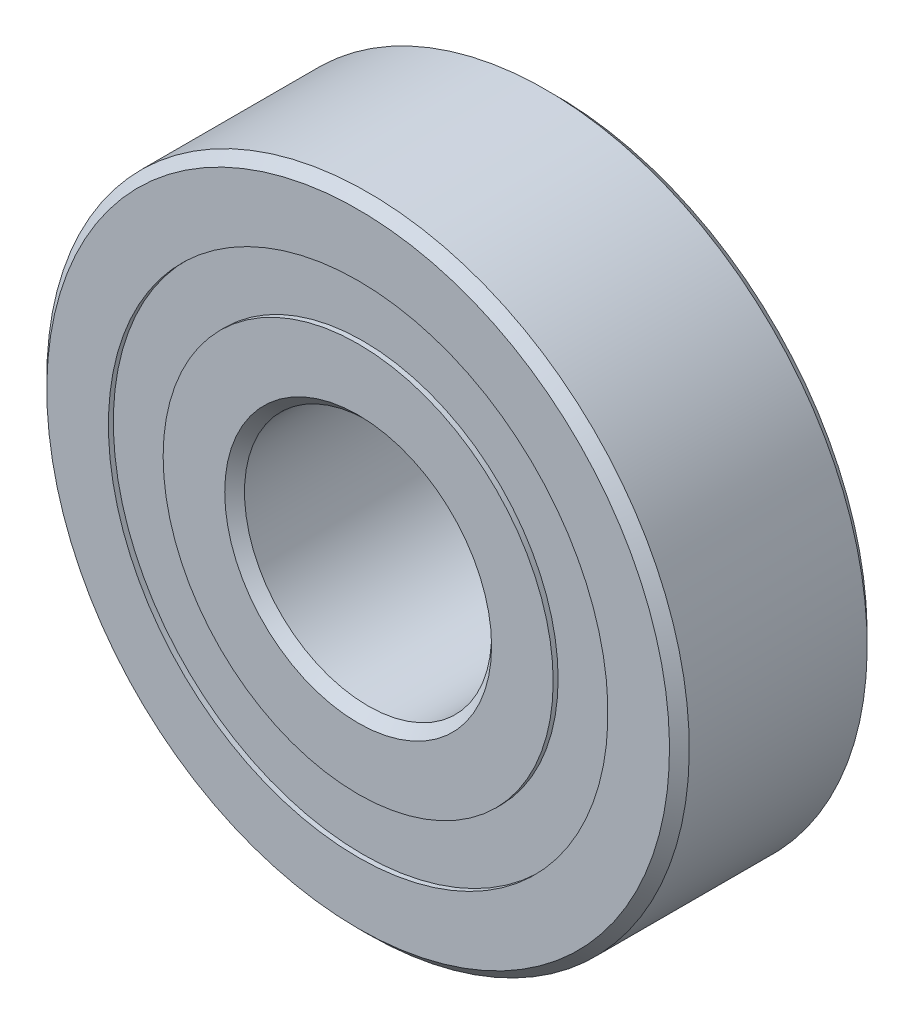
SolidWorks part; units mm, degrees
ref_plane "Front Plane" through (0, 0, 0) normal (0, 0, 1) x (1, 0, 0)
ref_plane "Top Plane" through (0, 0, 0) normal (0, 1, 0) x (1, 0, 0)
ref_plane "Right Plane" through (0, 0, 0) normal (1, 0, 0) x (0, 0, -1)
sketch "Sketch1" plane through (0, 0, 0) normal (0, 0, 1) x (1, 0, 0)
  line L0 (-13, 0) -> (13, 0) construction
  line L1 (-5, 0) -> (5, 0) construction
  circle A0 centre (0, 0) radius 5 construction
  circle A1 centre (0, 0) radius 13 construction
  point P3 (0, 0)
  point P6 (0, 0)
  point P7 (0, -5)
  point P11 (0, -13)
  point P12 (0, 5)
  point P13 (0, 13)
  dimension "OD" = 26
  dimension "ID" = 10
sketch "SketchB" plane through (0, 0, 0) normal (1, 0, 0) x (0, 0, -1)
  line L0 (-4, 13) -> (4, 13) construction
  line L1 (0, 13) -> (0, -13) construction
  line L2 (3.6, 13) -> (-3.6, 13)
  line L3 (-3.6, 13) -> (-4, 12.6)
  line L4 (-4, 12.6) -> (-4, 10.1077)
  line L5 (-4, 10.1077) -> (-1.7778, 10.1077)
  line L6 (4, 10.1077) -> (1.7778, 10.1077)
  line L7 (4, 12.6) -> (4, 10.1077)
  line L8 (3.6, 13) -> (4, 12.6)
  line L9 (0, 13) -> (0, 9) construction
  line L10 (0, 9) -> (0, 5) construction
  line L11 (0, 13) -> (0, -13) construction
  line L12 (-4, 0) -> (4, 0) construction
  line L13 (4, 5) -> (-4, 5) construction
  line L15 (-4, -5) -> (4, -5) construction
  arc A0 (-1.7778, 10.1077) -> (1.7778, 10.1077) centre (0, 9) cw
  circle A1 centre (0, 9) radius 2.0946 construction
  point P14 (0, 5)
  point P17 (0, 0)
  point P21 (0, 13)
  point P29 (0, 5)
  point P30 (0, -5)
  dimension "Width" = 8
  dimension "D1" = 45
  dimension "D2" = 0.4
  dimension "D3" = 3.5556
  dimension "D4" = 1.1077
sketch "Sketch7" plane through (0, 0, 0) normal (1, 0, 0) x (0, 0, -1)
  line L0 (3.6, 13) -> (4, 12.6) construction
  line L1 (4, 12.6) -> (4, 10.1077) construction
  line L2 (4, 10.1077) -> (1.7778, 10.1077) construction
  line L3 (-4, 10.1077) -> (-1.7778, 10.1077) construction
  line L4 (-4, 12.6) -> (-4, 10.1077) construction
  line L5 (-3.6, 13) -> (-4, 12.6) construction
  line L6 (3.6, 13) -> (-3.6, 13) construction
  line L7 (3.6, 13) -> (4, 12.6)
  line L8 (4, 12.6) -> (4, 10.1077)
  line L9 (4, 10.1077) -> (1.7778, 10.1077)
  line L10 (-4, 10.1077) -> (-1.7778, 10.1077)
  line L11 (-4, 12.6) -> (-4, 10.1077)
  line L12 (-3.6, 13) -> (-4, 12.6)
  line L13 (3.6, 13) -> (-3.6, 13)
  arc A0 (1.7778, 10.1077) -> (-1.7778, 10.1077) centre (0, 9) ccw construction
  arc A1 (1.7778, 10.1077) -> (-1.7778, 10.1077) centre (0, 9) ccw
revolve "Revolve6" add sketch "Sketch7" angle 360 about L12
sketch "Sketch3" plane through (0, 0, 0) normal (1, 0, 0) x (0, 0, -1)
  line L0 (0, 13) -> (0, -13) construction
  line L1 (0, 13) -> (0, -13) construction
  line L2 (-3.6, 5) -> (-4, 5.4)
  line L3 (-4, 5.4) -> (-4, 7.8923)
  line L5 (-4, 7.8923) -> (-1.7778, 7.8923)
  line L6 (-3.6, 5) -> (3.6, 5)
  line L8 (3.6, 5) -> (4, 5.4)
  line L10 (4, 5.4) -> (4, 7.8923)
  line L11 (4, 7.8923) -> (1.7778, 7.8923)
  line L12 (-4, 12.6) -> (-4, 10.1077) construction
  line L13 (3.6, 13) -> (4, 12.6) construction
  line L15 (4, -12.6) -> (4, 12.6) construction
  line L16 (3.6, 13) -> (3.6, -13) construction
  arc A1 (1.7778, 7.8923) -> (-1.7778, 7.8923) centre (0, 9) cw
  circle A2 centre (0, 9) radius 2.0946 construction
  point P1 (0, 5)
revolve "Revolve3" add sketch "Sketch3" angle 360 about L12
sketch "Sketch4" plane through (0, 0, 0) normal (1, 0, 0) x (0, 0, -1)
  line L0 (-2.0946, 9) -> (2.0946, 9)
  arc A2 (-2.0946, 9) -> (2.0946, 9) centre (0, 9) cw
  arc A3 (1.7778, 10.1077) -> (-1.7778, 10.1077) centre (0, 9) ccw construction
revolve "Revolve4" add sketch "Sketch4" angle 360 about L0
pattern_circular "CirPattern1" count 10 over 360 about axis through (0, 0, 0) along (0, 0, 1) of bodies 104
sketch "Sketch5" plane through (0, 0, 0) normal (1, 0, 0) x (0, 0, -1)
  line L0 (-4, 10.1077) -> (-1.7778, 10.1077) construction
  line L1 (-3.8, 10.1077) -> (-2.0946, 10.1077)
  line L2 (-3.8, 10.1077) -> (-3.8, 7.8923)
  line L3 (-3.8, 7.8923) -> (-2.0946, 7.8923)
  line L4 (-2.0946, 10.1077) -> (-2.0946, 7.8923)
  line L5 (-4, 7.8923) -> (-1.7778, 7.8923) construction
  line L6 (-3.6, 13) -> (-4, 12.6) construction
  line L7 (0, 13) -> (0, 5) construction
  line L8 (3.8, 7.8923) -> (2.0946, 7.8923)
  line L9 (2.0946, 10.1077) -> (2.0946, 7.8923)
  line L10 (3.8, 10.1077) -> (2.0946, 10.1077)
  line L11 (3.8, 10.1077) -> (3.8, 7.8923)
  circle A1 centre (0, 9) radius 2.0946 construction
  point P10 (-3.8, 12.8)
revolve "Revolve5" add sketch "Sketch5" angle 360 about L12
equation "\"D2@SketchB\" = \"Width@SketchB\" * .05"
equation "\"D3@SketchB\" = \"Width@SketchB\" / 2.25"
equation "\"D4@SketchB\" =  (  (  ( \"OD@Sketch1\" - \"Width@SketchB\" )  / 2 )  / 3.25 )  / 2.5"
